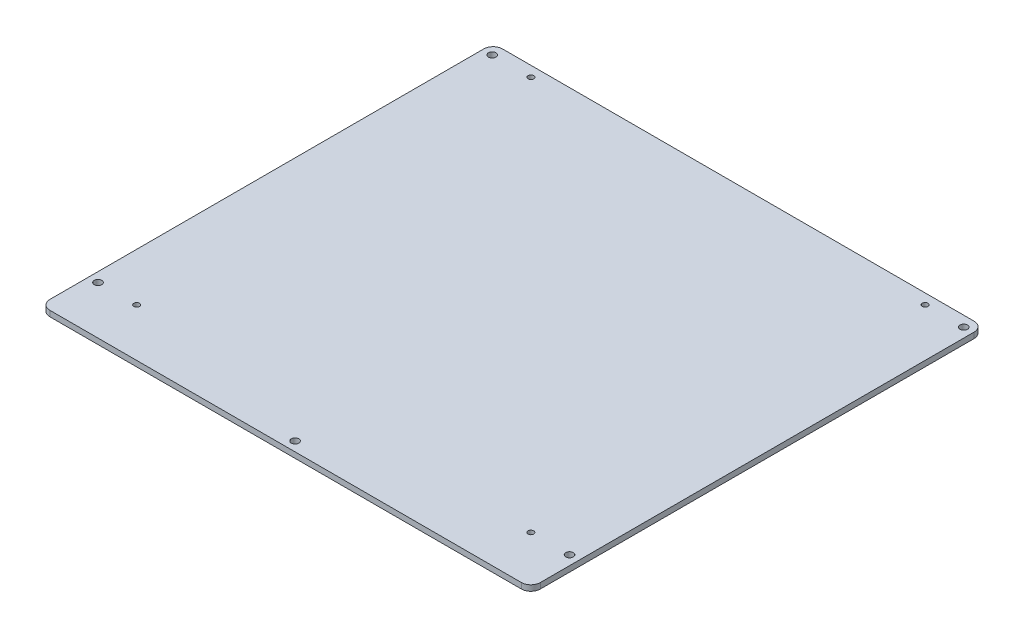
SolidWorks part; units mm, degrees
ref_plane "Alzado" through (0, 0, 0) normal (0, 0, 1) x (1, 0, 0)
ref_plane "Planta" through (0, 0, 0) normal (0, 1, 0) x (1, 0, 0)
ref_plane "Vista lateral" through (0, 0, 0) normal (1, 0, 0) x (0, 0, -1)
sketch "Croquis1" plane through (0, 0, 0) normal (0, 1, 0) x (1, 0, 0)
  line L0 (-163.2346, 0) -> (178.4444, 0) construction
  line L1 (-130, 110) -> (130, 110)
  line L2 (-130, 110) -> (-130, -130)
  line L3 (-130, -130) -> (130, -130)
  line L4 (130, 110) -> (130, -130)
  line L5 (0, 132.8148) -> (0, -144.7654) construction
  circle A0 centre (-104.5, 104.5) radius 1.5
  circle A1 centre (104.5, 104.5) radius 1.5
  circle A2 centre (-104.5, -104.5) radius 1.5
  circle A3 centre (104.5, -104.5) radius 1.5
  circle A4 centre (125, 104.5) radius 2
  circle A5 centre (125, -104.5) radius 2
  circle A6 centre (-125, -104.5) radius 2
  circle A7 centre (-125, 104.5) radius 2
  circle A8 centre (0, -125) radius 2
  dimension "D3" = 3
  dimension "D6" = 4
  dimension "D1" = 260
  dimension "D2" = 240
  dimension "D4" = 209
  dimension "D5" = 209
  dimension "D7" = 250
  dimension "D8" = 110
  dimension "D9" = 125
extrude "Saliente-Extruir1" add sketch "Croquis1" along normal blind 3
fillet "Redondeo1" radius 5 4 edges at (-130, 1.5, 130) (130, 1.5, 130) (130, 1.5, -110) (-130, 1.5, -110)
